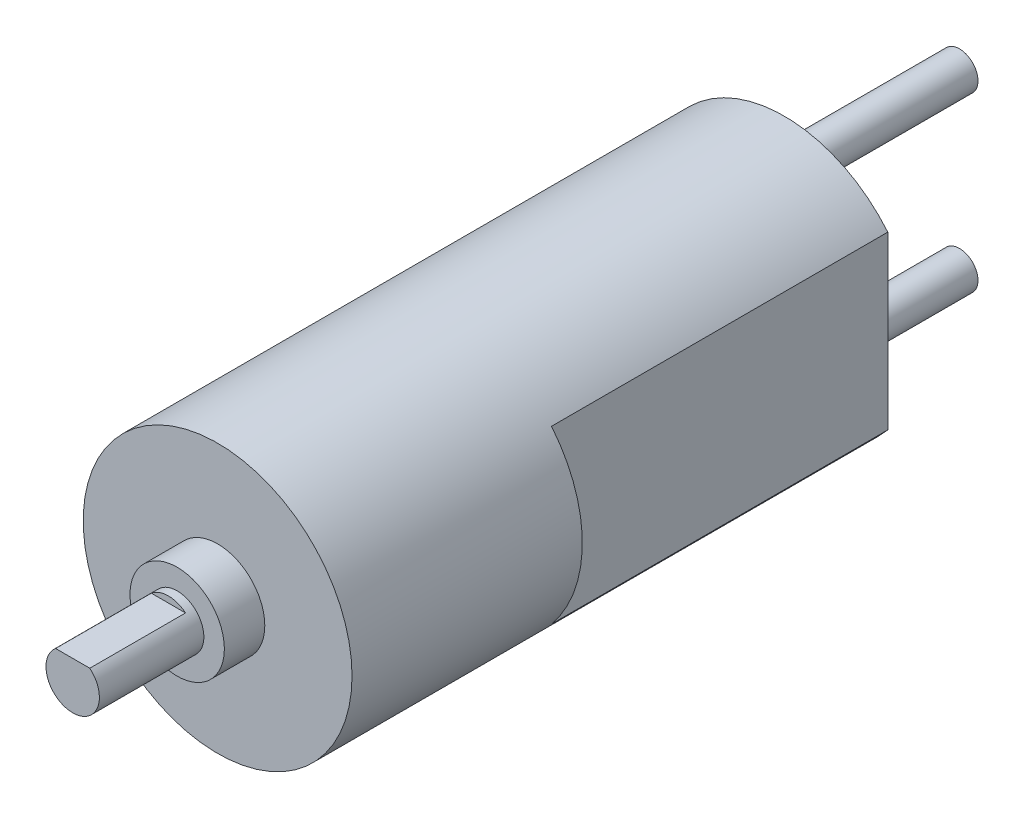
SolidWorks part; units mm, degrees
ref_plane "Front Plane" through (0, 0, 0) normal (0, 0, 1) x (1, 0, 0)
ref_plane "Top Plane" through (0, 0, 0) normal (0, 1, 0) x (1, 0, 0)
ref_plane "Right Plane" through (0, 0, 0) normal (1, 0, 0) x (0, 0, -1)
sketch "Sketch1" plane through (0, 0, 0) normal (0, 0, 1) x (1, 0, 0)
  circle A0 centre (0, 0) radius 9.9695
  dimension "D1" = 19.939
extrude "Boss-Extrude1" add sketch "Sketch1" along normal blind 17.0815
sketch "Sketch2" plane through (0, 0, 0) normal (0, 0, -1) x (-1, 0, 0)
  line L0 (0, 0) -> (7.6835, 0) construction
  line L1 (0, 0) -> (-7.6835, 0) construction
  line L2 (-7.6835, 6.3525) -> (-7.6835, -6.3525)
  line L3 (7.6835, 6.3525) -> (7.6835, -6.3525)
  circle A0 centre (0, 0) radius 9.9695 construction
  arc A1 (-7.6835, 6.3525) -> (7.6835, 6.3525) centre (0, 0) cw
  arc A2 (-7.6835, -6.3525) -> (7.6835, -6.3525) centre (0, 0) ccw
  dimension "D1" = 7.6835
extrude "Boss-Extrude2" add sketch "Sketch2" along normal blind 24.9428
sketch "Sketch3" plane through (0, 0, 17.0815) normal (0, 0, 1) x (1, 0, 0)
  circle A0 centre (0, 0) radius 3.5
  dimension "D1" = 7
extrude "Boss-Extrude3" add sketch "Sketch3" along normal blind 3
sketch "Sketch4" plane through (0, 0, 20.0815) normal (0, 0, 1) x (1, 0, 0)
  circle A0 centre (0, 0) radius 1.98
  dimension "D1" = 3.96
extrude "Boss-Extrude4" add sketch "Sketch4" along normal blind 7.75
sketch "Sketch5" plane through (0, 0, 27.8315) normal (0, 0, 1) x (1, 0, 0)
  line L0 (0, -1.98) -> (0, 1.52) construction
  line L1 (-1.2689, 1.52) -> (1.2689, 1.52)
  circle A0 centre (0, 0) radius 1.98 construction
  circle A1 centre (0, 0) radius 1.98 construction
  arc A2 (-1.2689, 1.52) -> (1.2689, 1.52) centre (0, 0) cw
  dimension "D1" = 1.2689
extrude "Cut-Extrude1" cut sketch "Sketch5" against normal blind 7.1
sketch "Sketch6" plane through (0, 0, -24.9428) normal (0, 0, -1) x (-1, 0, 0)
  circle A0 centre (0, 0) radius 3.01
  dimension "D1" = 6.02
extrude "Boss-Extrude5" add sketch "Sketch6" along normal blind 1.8
fillet "Fillet1" radius 0.5 1 edges at (-3.01, 0, -24.9428)
fillet "Fillet2" radius 0.1 1 edges at (-3.01, 0, -26.7428)
sketch "Sketch7" plane through (0, 0, -24.9428) normal (0, 0, -1) x (-1, 0, 0)
  line L0 (0, 2.91) -> (0, 6.41) construction
  line L1 (0, -2.91) -> (0, -6.41) construction
  circle A0 centre (0, 0) radius 2.91 construction
  circle A1 centre (0, 6.41) radius 1.375
  circle A2 centre (0, -6.41) radius 1.375
  dimension "D1" = 2.75
  dimension "D2" = 2.75
extrude "Boss-Extrude6" add sketch "Sketch7" along normal blind 13
